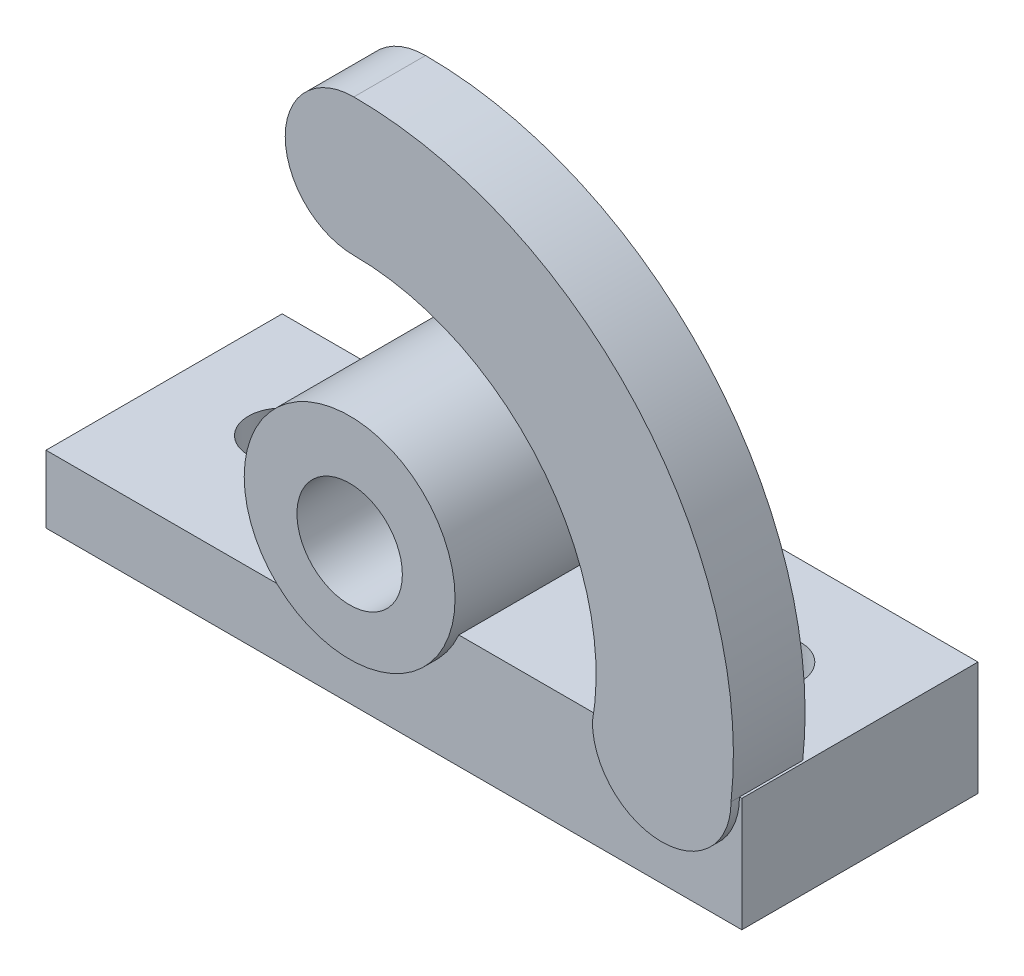
SolidWorks part; units mm, degrees
ref_plane "Front" through (0, 0, 0) normal (0, 0, 1) x (1, 0, 0)
ref_plane "Top" through (0, 0, 0) normal (0, 1, 0) x (1, 0, 0)
ref_plane "Right" through (0, 0, 0) normal (1, 0, 0) x (0, 0, -1)
sketch "Sketch1" plane through (0, 0, 0) normal (0, 1, 0) x (1, 0, 0)
  line L0 (0, 0) -> (0, 56)
  line L1 (0, 56) -> (165, 56)
  line L2 (165, 56) -> (165, 0)
  line L3 (165, 0) -> (0, 0)
  dimension "D1" = 165
  dimension "D2" = 56
extrude "Boss-Extrude1" add sketch "Sketch1" along normal blind 16
sketch "Sketch2" plane through (0, 16, 0) normal (0, 1, 0) x (1, 0, 0)
  circle A0 centre (25, 31) radius 8
  circle A1 centre (140, 31) radius 8
  point P4 (0, 0)
  dimension "D1" = 16
  dimension "D2" = 16
  dimension "D3" = 25
  dimension "D4" = 25
  dimension "D5" = 25
  dimension "D6" = 25
extrude "Cut-Extrude1" cut sketch "Sketch2" against normal blind 16 contours A0 | A1
sketch "Sketch3" plane through (0, 0, 0) normal (0, 0, 1) x (1, 0, 0)
  circle A0 centre (75, 37.0473) radius 25
  point P2 (76.2469, 36.747)
  point P3 (78.1175, 37.1343)
  point P5 (75, 37.0473)
  dimension "D1" = 50
  dimension "D2" = 90
extrude "Boss-Extrude2" add sketch "Sketch3" against normal blind 59 and the other way blind 3
fillet "Fillet1" radius 2 1 edges at (61.5089, 16, -28)
sketch "Sketch4" plane through (0, 0, 3) normal (0, 0, 1) x (1, 0, 0)
  circle A0 centre (75, 35.7137) radius 12.5
  point P2 (75, 35.7137)
  dimension "D1" = 25
  dimension "D2" = 90
extrude "Cut-Extrude2" cut sketch "Sketch4" against normal through all
sketch "Sketch5" plane through (0, 16, 0) normal (0, 1, 0) x (1, 0, 0)
  line L0 (88.4911, 0) -> (88.4911, 56)
  line L1 (88.4911, 0) -> (165, 0) construction
  line L2 (165, 56) -> (88.4911, 56) construction
  line L3 (88.4911, 56) -> (165, 56)
  line L4 (165, 56) -> (165, 0)
  line L5 (165, 0) -> (88.4911, 0)
  circle A0 centre (140, 31) radius 8
extrude "Boss-Extrude3" add sketch "Sketch5" along normal blind 11
ref_plane "Plane1" through (0, 60, 0) normal (0, 1, 0) x (1, 0, 0)
sketch "Sketch8" plane through (0, 0, 0) normal (0, 0, 1) x (1, 0, 0)
  line L0 (97.8922, 27) -> (165, 27) construction
  arc A0 (75, 127.0473) -> (164.4374, 27) centre (75, 37.0473) cw
  arc A1 (75, 94.4953) -> (131.5626, 27) centre (75, 37.0473) cw
  arc A2 (75, 127.0473) -> (75, 94.4953) centre (75, 110.7713) ccw
  arc A3 (131.5626, 27) -> (164.4374, 27) centre (148, 27) ccw
  point P2 (148.0958, 27)
  point P4 (0, 0)
  point P10 (0, 0)
  point P13 (0, 0)
  point P14 (148, 27)
  point P16 (0, 0)
  dimension "D1" = 90
extrude "Boss-Extrude5" add sketch "Sketch8" against normal blind 15 and the other way blind 2
sketch "Sketch9" plane through (0, 0, 2) normal (0, 0, 1) x (1, 0, 0)
  circle A0 centre (75, 111.8985) radius 7.6427
